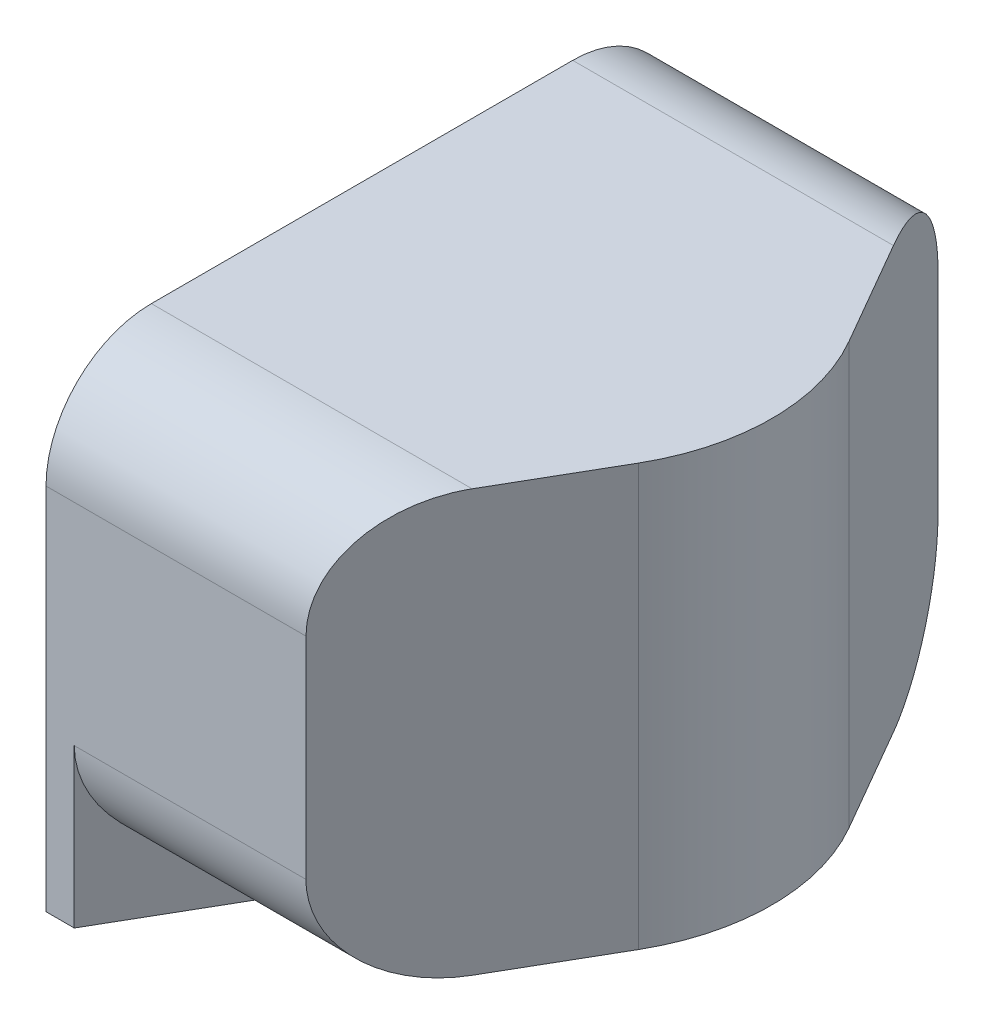
SolidWorks part; units mm, degrees
ref_plane "Front Plane" through (0, 0, 0) normal (0, 0, 1) x (1, 0, 0)
ref_plane "Top Plane" through (0, 0, 0) normal (0, 1, 0) x (1, 0, 0)
ref_plane "Right Plane" through (0, 0, 0) normal (1, 0, 0) x (0, 0, -1)
sketch "Sketch1" plane through (0, 0, 0) normal (1, 0, 0) x (0, 0, -1)
  line L1 (-3, -2) -> (3, -2)
  line L2 (-3, -2) -> (-3, 2)
  line L3 (-3, 2) -> (3, 2)
  line L4 (3, -2) -> (3, 2)
  line L5 (-3, -2) -> (3, 2) construction
  line L6 (-3, 2) -> (3, -2) construction
  point P0 (0, 0)
  dimension "D1" = 4
  dimension "D2" = 6
extrude "Boss-Extrude1" add sketch "Sketch1" against normal blind 4.2 from offset 23
sketch "Sketch2" plane through (0, 0, 0) normal (0, 1, 0) x (1, 0, 0)
  line L0 (0, 0) -> (23, 0) construction
  line L1 (22.4226, 1) -> (11.5, 19.9186)
  line L2 (11.5, 19.9186) -> (-11.5, 19.9186)
  line L3 (-11.5, 19.9186) -> (-23, 0)
  line L4 (-23, 0) -> (-11.5, -19.9186)
  line L5 (-11.5, -19.9186) -> (11.5, -19.9186)
  line L6 (11.5, -19.9186) -> (22.4226, -1)
  line L7 (11.5, 19.9186) -> (23, 19.9186)
  line L8 (23, 19.9186) -> (23, -19.9186)
  line L9 (23, -19.9186) -> (11.5, -19.9186)
  circle A0 centre (0, 0) radius 19.9186 construction
  arc A1 (22.4226, 1) -> (22.4226, -1) centre (20.6906, 0) cw
  dimension "D2" = 2
  dimension "D1" = 23
extrude "Cut-Extrude1" cut sketch "Sketch2" along normal through all both and the other way through all contours L1 A1 L6 L9 L8 L7
sketch "Sketch4" plane through (18.8, 0, 0) normal (-1, 0, 0) x (0, 0, 1)
  line L0 (-4, 3) -> (-4, -3)
  line L1 (-4, -3) -> (4, -3)
  line L2 (4, -3) -> (4, 3)
  line L3 (4, 3) -> (-4, 3)
  line L4 (-3, 2) -> (-3, -2)
  line L5 (-3, -2) -> (3, -2)
  line L6 (3, -2) -> (3, 2)
  line L7 (3, 2) -> (-3, 2)
  line L8 (-3, 2) -> (-3, -2)
  line L9 (-3, -2) -> (3, -2)
  line L10 (3, -2) -> (3, 2)
  line L11 (3, 2) -> (-3, 2)
  dimension "D1" = 0
  dimension "D2" = 1
sketch "Sketch5" plane through (0, 0, 0) normal (0, 1, 0) x (1, 0, 0)
  line L0 (0, 0) -> (20.8, 0) construction
  line L1 (20.8, 0) -> (19.0679, 3)
  line L2 (10.4, 18.0133) -> (-10.4, 18.0133)
  line L3 (-10.4, 18.0133) -> (-20.8, 0)
  line L4 (-20.8, 0) -> (-10.4, -18.0133)
  line L5 (-10.4, -18.0133) -> (10.4, -18.0133)
  line L6 (10.4, -18.0133) -> (15.6, -9.0067)
  line L7 (15.6, 9.0067) -> (10.4, 18.0133)
  line L10 (18.8, 3) -> (18.8, -3)
  line L11 (19.0679, -3) -> (20.8, 0)
  line L17 (22.4226, 1) -> (21.2679, 3)
  line L18 (21.2679, 3) -> (18.8, 3)
  line L19 (18.8, 3) -> (18.8, -3)
  line L20 (18.8, -3) -> (21.2679, -3)
  line L21 (21.2679, -3) -> (22.4226, -1)
  line L22 (22.4226, 1) -> (21.2679, 3)
  line L23 (21.2679, 3) -> (18.8, 3)
  line L24 (18.8, 3) -> (18.8, -3)
  line L25 (18.8, -3) -> (21.2679, -3)
  line L26 (21.2679, -3) -> (22.4226, -1)
  circle A0 centre (0, 0) radius 18.0133 construction
  arc A2 (22.4226, -1) -> (22.4226, 1) centre (20.6906, 0) ccw
  arc A3 (22.4226, -1) -> (22.4226, 1) centre (20.6906, 0) ccw
  dimension "D1" = 20.8
  dimension "D2" = 0
extrude "Boss-Extrude3" add sketch "Sketch5" along normal blind 2 and the other way blind 2.5
fillet "Fillet2" radius 1 4 edges at (20.034, 2, -3) (20.1679, -2, -3) (20.1679, -2, 3) (20.034, 2, 3)
